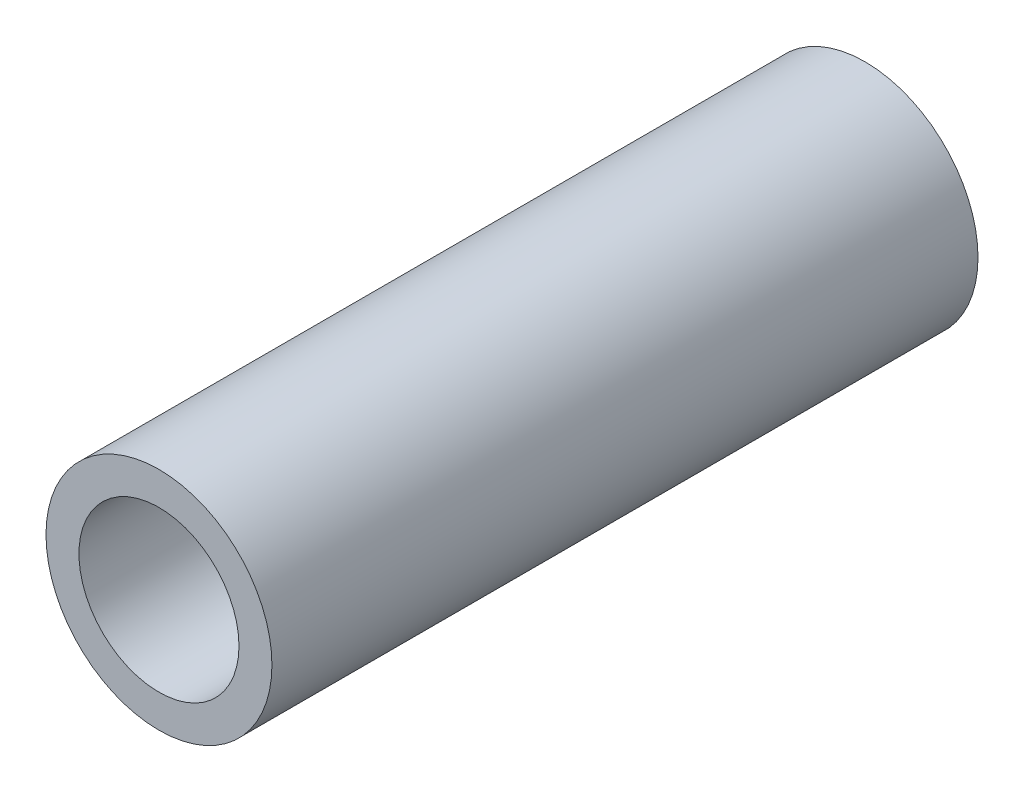
SolidWorks part; units mm, degrees
ref_plane "Front Plane" through (0, 0, 0) normal (0, 0, 1) x (1, 0, 0)
ref_plane "Top Plane" through (0, 0, 0) normal (0, 1, 0) x (1, 0, 0)
ref_plane "Right Plane" through (0, 0, 0) normal (1, 0, 0) x (0, 0, -1)
sketch "Sketch1" plane through (0, 0, 0) normal (0, 0, 1) x (1, 0, 0)
  circle A0 centre (0, 0) radius 8.5
  circle A1 centre (0, 0) radius 12
  dimension "D1" = 17
  dimension "D2" = 24
extrude "Boss-Extrude1" add sketch "Sketch1" along normal mid plane 75
